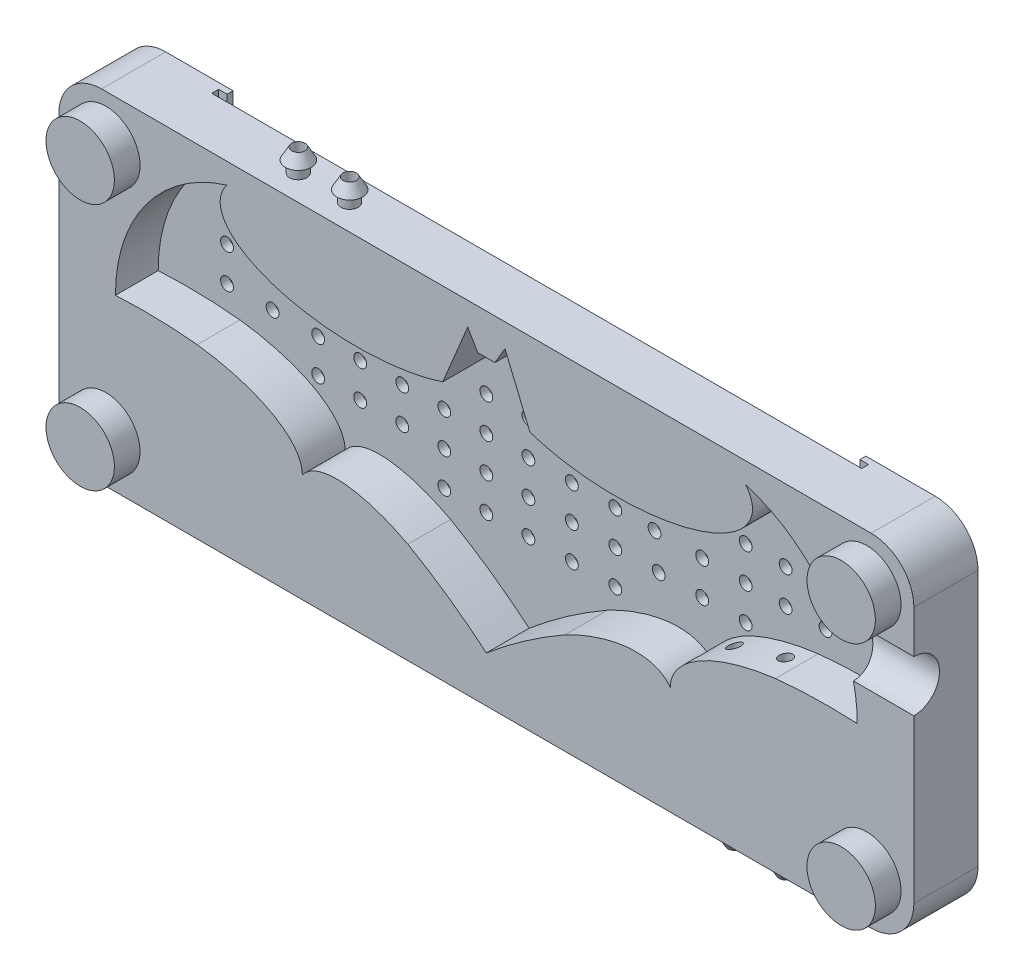
SolidWorks part; units mm, degrees
ref_plane "Alzado" through (0, 0, 0) normal (0, 0, 1) x (1, 0, 0)
ref_plane "Planta" through (0, 0, 0) normal (0, 1, 0) x (1, 0, 0)
ref_plane "Vista lateral" through (0, 0, 0) normal (1, 0, 0) x (0, 0, -1)
sketch "Croquis2" plane through (0, 0, 0) normal (0, 0, 1) x (1, 0, 0)
  line L1 (-25, 20) -> (25, 20)
  line L2 (-25, 20) -> (-25, -20)
  line L3 (-25, -20) -> (25, -20)
  line L4 (25, 20) -> (25, -20)
  line L5 (-25, 20) -> (25, -20) construction
  line L6 (-25, -20) -> (25, 20) construction
  point P0 (0, 0)
  dimension "D1" = 50
  dimension "D2" = 40
extrude "Saliente-Extruir1" add sketch "Croquis2" along normal blind 7.5
sketch "Croquis3" plane through (0, 0, 7.5) normal (0, 0, 1) x (1, 0, 0)
  line L0 (25, 20) -> (-25, 20) construction
  line L1 (25, -20) -> (25, 20) construction
  line L2 (-18.3764, 0) -> (25, -14.6291) construction
  line L3 (19.9012, 10.2799) -> (22.822, 17.2799)
  line L4 (22.822, 17.2799) -> (24, 15.2799)
  line L5 (24, 15.2799) -> (25, 15.2799)
  line L6 (25, 15.2799) -> (25, -14.6291)
  arc A0 (-5.3342, 17.5852) -> (-18.3761, -0.092) centre (0, 0) ccw
  arc A1 (-8.8163, -0.3091) -> (-18.3761, -0.092) centre (-15, -62) ccw
  arc A2 (25, -14.6291) -> (15.8176, -8.2016) centre (-15, -62) ccw
  ellipse E0 centre (9.8712, 15.5) end of major axis (-6.1288, 15.5) minor radius 6.7 (-5.3342, 17.5852) -> (19.9012, 10.2799) ccw
  ellipse E1 centre (-13.5194, -7.3146) end of major axis (-30.5194, -7.2576) minor radius 7.3033 (3.4806, -7.3715) -> (-8.8163, -0.3091) ccw
  ellipse E2 centre (15.6413, -16.1532) end of major axis (3.4806, -7.3715) minor radius 6.8678 (15.8176, -8.2016) -> (3.4806, -7.3715) ccw
  dimension "D1" = 36.7528
  dimension "D6" = 82
  dimension "D7" = 124
  dimension "D2" = 8.8
  dimension "D3" = 15.5
  dimension "D4" = 6.7
  dimension "D5" = 16
  dimension "D8" = 40
  dimension "D9" = 17
  dimension "D10" = 15
  dimension "D11" = 7.3032
  dimension "D12" = 5.5678
  dimension "D13" = 7.3715
  dimension "D14" = 8.7817
  dimension "D15" = 14.1807
  dimension "D16" = 7
  dimension "D17" = 1
  dimension "D18" = 12.9508
  dimension "D19" = 10.03
  dimension "D20" = 5
extrude "Cortar-Extruir1" cut sketch "Croquis3" against normal blind 5
mirror "Simetría1" about plane through (25, 20, 7.5) normal (-1, 0, 0) of "Cortar-Extruir1", "Saliente-Extruir1"
ref_plane "Plano1" through (0, 0, 15) normal (0, 0, 1) x (1, 0, 0)
sketch "Croquis4" plane through (0, 0, 7.5) normal (0, 0, 1) x (1, 0, 0)
  line L0 (5.775, 0) -> (-5.775, 0) construction
  line L1 (-25, 20) -> (-25, -20) construction
  line L2 (75, 20) -> (75, -20) construction
  line L3 (-25, -20) -> (75, -20) construction
  circle A0 centre (-19.5, 14.5) radius 4
  circle A1 centre (69.5, 14.5) radius 4
  circle A2 centre (-19.5, -14.5) radius 4
  circle A3 centre (69.5, -14.5) radius 4
  dimension "D1" = 2
  dimension "D3" = 8
  dimension "D4" = 5.5
  dimension "D5" = 34.5
  dimension "D2" = 5.5
extrude "Saliente-Extruir2" add sketch "Croquis4" along normal blind 3
fillet "Redondeo1" radius 5 4 edges at (-25, -20, 3.75) (-25, 20, 3.75) (75, -20, 3.75) (75, 20, 3.75)
sketch "Croquis5" plane through (0, 20, 0) normal (0, 1, 0) x (1, 0, 0)
  line L0 (70, -7.5) -> (-20, -7.5) construction
  line L1 (0, -7.5) -> (12.5, -7.5)
  line L2 (0, -7.5) -> (0, 0)
  line L3 (0, 0) -> (12.5, 0)
  line L4 (12.5, -7.5) -> (12.5, 0)
  line L5 (70, 0) -> (-20, 0) construction
  line L6 (-20, 0) -> (-20, -7.5) construction
  line L8 (70, -7.5) -> (70, 0) construction
  line L9 (37.5, 0) -> (50, 0)
  line L10 (37.5, 0) -> (37.5, -7.5)
  line L11 (37.5, -7.5) -> (50, -7.5)
  line L12 (50, 0) -> (50, -7.5)
  dimension "D1" = 12.5
  dimension "D2" = 20
  dimension "D3" = 12.5
  dimension "D4" = 20
sketch "Croquis8" plane through (75, 0, 0) normal (1, 0, 0) x (0, 0, -1)
  line L0 (-7.5, 15) -> (-7.5, -15) construction
  line L1 (-7.5, 4) -> (-7.5, 10)
  arc A0 (-7.5, 4) -> (-7.5, 10) centre (-7.5, 7) ccw
  dimension "D1" = 8
  dimension "D2" = 6
extrude "Cortar-Extruir3" cut sketch "Croquis8" against normal blind 10
ref_plane "Plano2" through (0, 2.6, 0) normal (0, -1, 0) x (-1, 0, 0)
ref_plane "Plano3" through (25, 0, 0) normal (1, 0, 0) x (0, 0, -1)
sketch "Croquis9" plane through (0, 0, 0) normal (0, 0, -1) x (-1, 0, 0)
  line L0 (-60.3523, 2.6) -> (-44.4971, 2.6) construction
  line L1 (-11.8322, 2.6) -> (11.8322, 2.6) construction
  line L2 (-44.25, 2.6) -> (16.4783, 2.6) construction
  line L3 (-24.9176, 17.9687) -> (-24.9176, -8.5454) construction
  line L4 (-75, 15) -> (-75, 10) construction
  line L5 (-75, 4) -> (-75, -15) construction
  line L6 (25, 15) -> (25, -15) construction
  line L7 (20, -20) -> (-70, -20) construction
  line L8 (-70, 20) -> (20, 20) construction
  circle A0 centre (-24.9176, 2.6) radius 0.75
  circle A1 centre (-24.9176, -1.4) radius 0.75
  circle A2 centre (-24.9176, 6.6) radius 0.75
  circle A3 centre (-24.9176, 10.6) radius 0.75
  circle A4 centre (-24.9176, -5.4) radius 0.75
  circle A5 centre (-20, 2.6) radius 0.75
  circle A6 centre (-20, -1.4) radius 0.75
  circle A7 centre (-20, 6.6) radius 0.75
  circle A8 centre (-15.0824, 2.6) radius 0.75
  circle A9 centre (-15.0824, -1.4) radius 0.75
  circle A10 centre (-15.0824, 6.6) radius 0.75
  circle A11 centre (-10.1647, 2.6) radius 0.75
  circle A12 centre (-10.1647, -1.4) radius 0.75
  circle A13 centre (-10.1647, 6.6) radius 0.75
  circle A14 centre (-5.2471, 2.6) radius 0.75
  circle A15 centre (-5.2471, -1.4) radius 0.75
  circle A16 centre (-5.2471, 6.6) radius 0.75
  circle A17 centre (-0.3294, 2.6) radius 0.75
  circle A18 centre (-0.3294, -1.4) radius 0.75
  circle A19 centre (-0.3294, 6.6) radius 0.75
  circle A20 centre (-30, 2.6) radius 0.75
  circle A21 centre (-30, -1.4) radius 0.75
  circle A22 centre (-30, 6.6) radius 0.75
  circle A23 centre (-35.0824, 2.6) radius 0.75
  circle A24 centre (-35.0824, -1.4) radius 0.75
  circle A25 centre (-35.0824, 6.6) radius 0.75
  circle A27 centre (-40.1647, -1.4) radius 0.75
  circle A29 centre (-45.2471, 2.6) radius 0.75
  circle A30 centre (-45.2471, -1.4) radius 0.75
  circle A32 centre (-50.3294, 2.6) radius 0.75
  circle A33 centre (-50.3294, -1.4) radius 0.75
  circle A34 centre (-50.3294, 6.6) radius 0.75
  circle A35 centre (-20, -5.4) radius 0.75
  circle A36 centre (-30, -5.4) radius 0.75
  circle A37 centre (-15.0824, -5.4) radius 0.75
  circle A38 centre (-35.0824, -5.4) radius 0.75
  circle A39 centre (-55, 6.6) radius 0.75
  circle A40 centre (-55, 2.6) radius 0.75
  circle A41 centre (-59.6706, 6.6) radius 0.75
  circle A42 centre (-59.6706, 2.6) radius 0.75
  circle A43 centre (-45, 6.6) radius 0.75
  circle A45 centre (5, 6.6) radius 0.75
  circle A46 centre (5, 2.6) radius 0.75
  circle A47 centre (-39.6706, 6.6) radius 0.75
  circle A48 centre (-39.6706, 2.6) radius 0.75
  circle A49 centre (10.3294, 6.6) radius 0.75
  circle A50 centre (10.3294, 2.6) radius 0.75
  circle A51 centre (10.3294, 10.6) radius 0.75
  circle A52 centre (-59.6706, 10.6) radius 0.75
  arc A53 (-39.9176, 5.8919) -> (-39.9176, 7.3081) centre (-40.1647, 6.6) ccw [skipped]
  arc A54 (-45.1235, 7.3398) -> (-45.1235, 5.8602) centre (-45.2471, 6.6) ccw [skipped]
  arc A55 (-45.1235, 3.3398) -> (-45.75, 2.6) centre (-45, 2.6) ccw [skipped]
  arc A56 (-39.9176, 1.8919) -> (-39.4147, 2.6) centre (-40.1647, 2.6) ccw [skipped]
  dimension "D1" = 1.5
  dimension "D2" = 1.5
  dimension "D3" = 1.5
  dimension "D4" = 1.5
  dimension "D5" = 4
  dimension "D6" = 4
  dimension "D7" = 4
  dimension "D8" = 1.5
  dimension "D9" = 4
  dimension "D16" = 50.0824
  dimension "D17" = 45
  dimension "D18" = 45
  dimension "D19" = 14.6
  dimension "D20" = 20
  dimension "D21" = 20
  dimension "D22" = 9.4
  dimension "D10" = 6
  dimension "D11" = 6
  dimension "D12" = 2
  dimension "D14" = 3
  dimension "D13" = 3
  dimension "D15" = 2
extrude "Cortar-Extruir4" cut sketch "Croquis9" against normal up to next (2.5 mm away)
sketch "Croquis10" plane through (0, 20, 0) normal (0, 1, 0) x (1, 0, 0)
  line L3 (-12.1142, -0.7) -> (-13.1142, -0.7)
  line L5 (70, 0) -> (-20, 0) construction
  line L8 (61.8858, -0.7) -> (62.8858, -0.7)
  line L10 (-13.1142, -0.7) -> (-12.1142, -0.7)
  line L11 (-13.1142, -0.7) -> (-13.1142, -1.5)
  line L12 (-13.1142, -1.5) -> (62.8858, -1.5)
  line L13 (62.8858, -0.7) -> (62.8858, -1.5)
  line L14 (61.8858, -0.7) -> (62.8858, -0.7)
  line L15 (-12.1142, 0) -> (61.8858, 0)
  line L16 (-12.1142, 0) -> (-12.1142, -0.7)
  line L18 (61.8858, 0) -> (61.8858, -0.7)
  line L19 (-20, 0) -> (-20, -7.5) construction
  line M8 (70, 0) -> (-20, 0)
  dimension "D1" = 76
  dimension "D2" = 6.8858
  dimension "D3" = 0.8
  dimension "D4" = 0.7
  dimension "D5" = 1
  dimension "D6" = 1
extrude "Cortar-Extruir5" cut sketch "Croquis10" against normal blind 30 contours L18 L16 L3 L11 L12 L13 L8 M8
sketch "Croquis14" plane through (0, 20, 0) normal (0, 1, 0) x (1, 0, 0)
  line L0 (-13.1142, -1.5) -> (62.8858, -1.5) construction
  line L2 (-20, 0) -> (-20, -7.5) construction
  circle A0 centre (0, -4.5) radius 0.75
  circle A1 centre (6, -4.5) radius 0.75
  dimension "D1" = 1.5
  dimension "D2" = 3
  dimension "D3" = 20
  dimension "D5" = 6
  dimension "D4" = 2
extrude "Cortar-Extruir6" cut sketch "Croquis14" against normal up to next
sketch "Croquis15" plane through (0, -20, 0) normal (0, -1, 0) x (1, 0, 0)
  line L0 (-20, 7.5) -> (70, 7.5) construction
  line L1 (70, 0) -> (70, 7.5) construction
  circle A0 centre (57, 4.5) radius 0.75
  circle A1 centre (51, 4.5) radius 0.75
  dimension "D1" = 1.5
  dimension "D2" = 3
  dimension "D3" = 13
  dimension "D5" = 6
  dimension "D4" = 2
extrude "Cortar-Extruir7" cut sketch "Croquis15" against normal up to next
sketch "Croquis16" plane through (0, -20, 0) normal (0, -1, 0) x (1, 0, 0)
  circle A0 centre (51, 4.5) radius 1
  circle A1 centre (57, 4.5) radius 1
  circle A2 centre (51, 4.5) radius 0.75
  circle A3 centre (57, 4.5) radius 0.75
  dimension "D1" = 2
  dimension "D2" = 2
  dimension "D3" = 1.5
  dimension "D4" = 1.5
extrude "Saliente-Extruir6" add sketch "Croquis16" along normal blind 1.3
sketch "Croquis25" plane through (0, -21.3, 0) normal (0, -1, 0) x (1, 0, 0)
  line L0 (51, 3.5) -> (51, 5.5) construction
  line L1 (57, 3.5) -> (57, 5.5) construction
  circle A0 centre (51, 4.5) radius 1 construction
  circle A1 centre (51, 4.5) radius 1 construction
  circle A2 centre (57, 4.5) radius 1 construction
  circle A3 centre (57, 4.5) radius 1 construction
ref_plane "Plano4" through (51, 0, 0) normal (1, 0, 0) x (0, 0, -1)
sketch "Croquis26" plane through (51, 0, 0) normal (1, 0, 0) x (0, 0, -1)
  line L0 (-3.75, -21.3) -> (-3.75, -22.599)
  line L1 (-3.75, -22.599) -> (-3, -21.3)
  line L2 (-3, -21.3) -> (-3.5, -21.3)
  line L3 (-3.5, -21.3) -> (-3.75, -21.3)
  line L4 (-4.5, -21.3) -> (-4.5, -23.0571) construction
  line L5 (-3.5, -21.3) -> (-5.5, -21.3) construction
  dimension "D1" = 0.5
  dimension "D2" = 1.5
revolve "Revolución1" add sketch "Croquis26" angle 360 about L4
pattern_linear "MatrizL1" count 2 spacing 6 along (1, 0, 0) of "Revolución1"
sketch "Croquis27" plane through (0, 20, 0) normal (0, 1, 0) x (1, 0, 0)
  circle A0 centre (0, -4.5) radius 1
  circle A1 centre (6, -4.5) radius 1
  circle A2 centre (0, -4.5) radius 0.75
  circle A3 centre (6, -4.5) radius 0.75
  dimension "D1" = 2
  dimension "D2" = 2
  dimension "D3" = 1.5
  dimension "D4" = 1.5
extrude "Saliente-Extruir11" add sketch "Croquis27" along normal blind 1.3
sketch "Croquis28" plane through (0, 21.3, 0) normal (0, 1, 0) x (1, 0, 0)
  line L0 (0, -5.25) -> (0, -3.7186) construction
  circle A0 centre (0, -4.5) radius 0.75 construction
ref_plane "Plano5" through (0, 0, 0) normal (-1, 0, 0) x (0, 0, 1)
sketch "Croquis29" plane through (0, 0, 0) normal (-1, 0, 0) x (0, 0, 1)
  line L0 (5.5, 21.3) -> (6, 21.3)
  line L1 (5.2586, 21.3) -> (5.2586, 22.604)
  line L2 (5.25, 21.3) -> (3.7186, 21.3) construction
  line L3 (5.5, 21.3) -> (3.5, 21.3) construction
  line L4 (5.2586, 22.604) -> (6, 21.3)
  line L5 (5.5, 21.3) -> (5.2586, 21.3)
  line L6 (4.4843, 21.3) -> (4.4843, 22.8455) construction
  dimension "D1" = 0.5
  dimension "D2" = 1.5
  dimension "D3" = 1.304
revolve "Revolución2" add sketch "Croquis29" angle 360 about L6
pattern_linear "MatrizL2" count 2 spacing 6 along (1, 0, 0) of "Revolución2"
